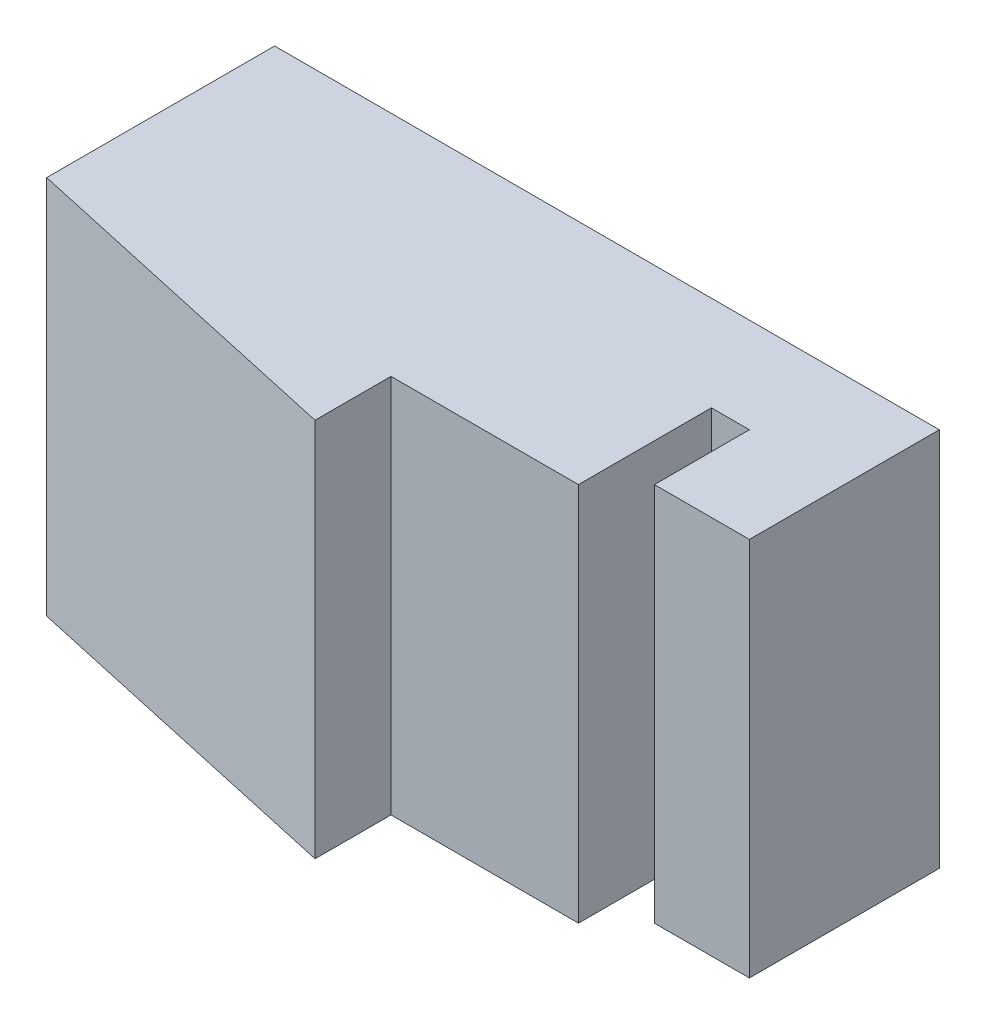
SolidWorks part; units mm, degrees
ref_plane "Front Plane" through (0, 0, 0) normal (0, 0, 1) x (1, 0, 0)
ref_plane "Top Plane" through (0, 0, 0) normal (0, 1, 0) x (1, 0, 0)
ref_plane "Right Plane" through (0, 0, 0) normal (1, 0, 0) x (0, 0, -1)
sketch "Sketch1" plane through (0, 0, 0) normal (0, 1, 0) x (1, 0, 0)
  line L0 (-27.629, 0) -> (7.371, 0)
  line L1 (7.371, 0) -> (7.371, -10)
  line L2 (7.371, -10) -> (2.371, -10)
  line L3 (-27.629, 0) -> (-27.629, -12)
  line L4 (2.371, -10) -> (2.371, -5)
  line L5 (-9.5, -12) -> (-9.5, -16)
  line L6 (-9.5, -16) -> (-27.629, -12)
  line L7 (2.371, -5) -> (0.371, -5)
  line L8 (0.371, -5) -> (0.371, -12)
  line L9 (0.371, -12) -> (-9.5, -12)
extrude "Boss-Extrude1" add sketch "Sketch1" along normal blind 20
